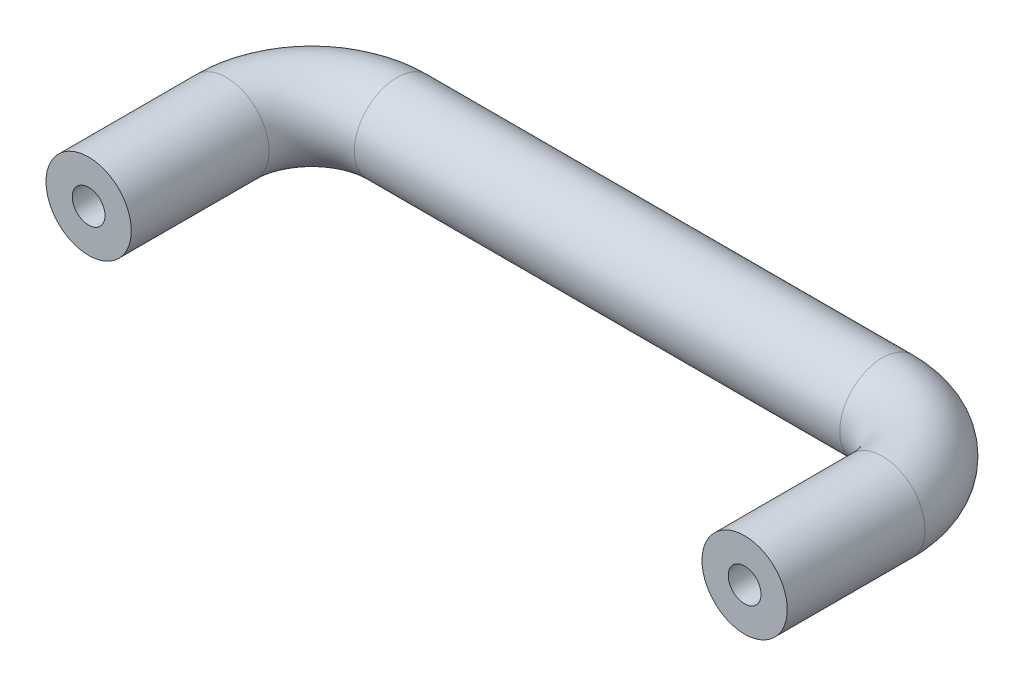
SolidWorks part; units mm, degrees
material "1060 Alloy"
ref_plane "Front Plane" through (0, 0, 0) normal (0, 0, 1) x (1, 0, 0)
ref_plane "Top Plane" through (0, 0, 0) normal (0, 1, 0) x (1, 0, 0)
ref_plane "Right Plane" through (0, 0, 0) normal (1, 0, 0) x (0, 0, -1)
sketch "Sketch1" plane through (0, 0, 0) normal (0, 1, 0) x (1, 0, 0)
  line L0 (-50, -34) -> (-50, -13)
  line L1 (-37, 0) -> (37, 0)
  line L2 (50, -13) -> (50, -34)
  arc A0 (37, 0) -> (50, -13) centre (37, -13) cw
  arc A1 (-50, -13) -> (-37, 0) centre (-37, -13) cw
  point P7 (50, 0)
  point P10 (-50, 0)
  dimension "D3" = 13
  dimension "D1" = 100
  dimension "D2" = 34
sweep "Sweep1" add path "Sketch1" circular profile diameter 13 parameters "D3"=13
hole_wizard "Tap Drill for M6x1.0 Tap1" positions "Sketch14" profile "Sketch15" hole size "M6x1.0" standard "ANSI Metric"
sketch "Sketch14" plane through (0, 0, 34) normal (0, 0, 1) x (1, 0, 0)
  point P0 (-50, 0)
  point P3 (50, 0)
sketch "Sketch15" plane through (-50, 0, 34) normal (1, 0, 0) x (0, -1, 0)
  line L0 (0, 0) -> (0, 23.5022)
  line L1 (0, 23.5022) -> (2.5, 22)
  line L2 (2.5, 22) -> (2.5, 0)
  line L5 (2.5, 0) -> (0, 0)
  line L10 (0, 23.5022) -> (-2.5, 22) construction
  line L11 (0, -6.35) -> (0, 107.95) construction
  dimension "Hole Dia." = 5
  dimension "Hole Depth" = 22
  dimension "Drill Angle" = 118
